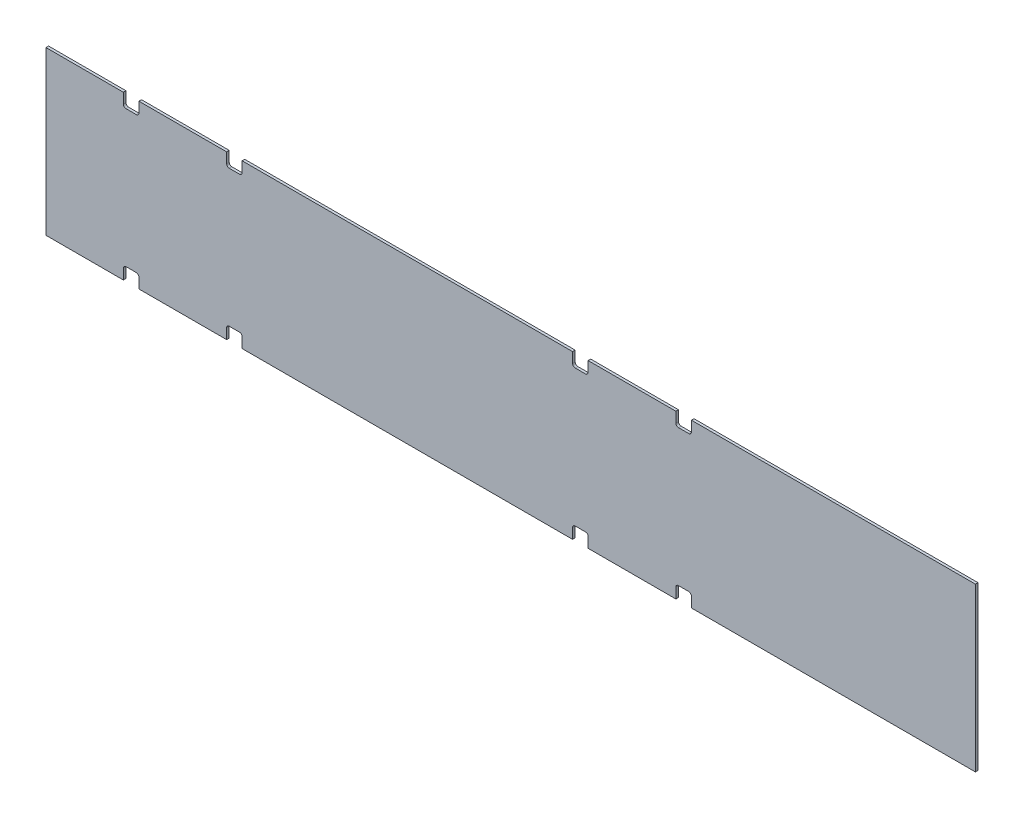
SolidWorks part; units mm, degrees
material "PC High Viscosity"
ref_plane "Front Plane" through (0, 0, 0) normal (0, 0, 1) x (1, 0, 0)
ref_plane "Top Plane" through (0, 0, 0) normal (0, 1, 0) x (1, 0, 0)
ref_plane "Right Plane" through (0, 0, 0) normal (1, 0, 0) x (0, 0, -1)
sketch "Sketch1" plane through (0, 0, 0) normal (0, 0, 1) x (1, 0, 0)
  line L1 (-571.5, -100.0125) -> (571.5, -100.0125)
  line L2 (-571.5, -100.0125) -> (-571.5, 100.0125)
  line L3 (-571.5, 100.0125) -> (571.5, 100.0125)
  line L4 (571.5, -100.0125) -> (571.5, 100.0125)
  line L5 (-571.5, -100.0125) -> (571.5, 100.0125) construction
  line L6 (-571.5, 100.0125) -> (571.5, -100.0125) construction
  point P0 (0, 0)
  dimension "D1" = 1143
  dimension "D2" = 200.025
extrude "Boss-Extrude1" add sketch "Sketch1" along normal blind 3.175
sketch "Sketch3" plane through (0, 0, 3.175) normal (0, 0, 1) x (1, 0, 0)
  line L0 (-571.5, -100.0125) -> (571.5, -100.0125) construction
  line L1 (-476.3389, -100.0125) -> (-457.2889, -100.0125)
  line L2 (-476.3389, -100.0125) -> (-476.3389, -84.1375)
  line L3 (-476.3389, -84.1375) -> (-457.2889, -84.1375)
  line L4 (-349.3389, -100.0125) -> (-349.3389, -84.1375)
  line L5 (-349.3389, -100.0125) -> (-330.2889, -100.0125)
  line L6 (-457.2889, -100.0125) -> (-457.2889, -84.1375)
  line L7 (-571.5, 100.0125) -> (-571.5, -100.0125) construction
  line L8 (-330.2889, -100.0125) -> (-330.2889, -84.1375)
  line L9 (-349.3389, -84.1375) -> (-330.2889, -84.1375)
  line L10 (-476.3389, -100.0125) -> (-349.3389, -100.0125) construction
  line L11 (76.1111, -100.0125) -> (76.1111, -84.1375)
  line L12 (76.1111, -100.0125) -> (95.1611, -100.0125)
  line L13 (95.1611, -100.0125) -> (95.1611, -84.1375)
  line L14 (76.1111, -84.1375) -> (95.1611, -84.1375)
  line L15 (203.1111, -100.0125) -> (203.1111, -84.1375)
  line L16 (203.1111, -84.1375) -> (222.1611, -84.1375)
  line L17 (222.1611, -100.0125) -> (222.1611, -84.1375)
  line L18 (203.1111, -100.0125) -> (222.1611, -100.0125)
  line L19 (-476.3389, -100.0125) -> (76.1111, -100.0125) construction
  point P6 (-466.8139, -100.0125)
  dimension "D1" = 15.875
  dimension "D2" = 19.05
  dimension "D3" = 104.6861
  dimension "D4" = 2
  dimension "D5" = 127
  dimension "D6" = 2
  dimension "D7" = 552.45
extrude "Cut-Extrude1" cut sketch "Sketch3" against normal through all
fillet "Fillet1" radius 3.175 8 edges at (222.1611, -84.1375, 1.5875) (203.1111, -84.1375, 1.5875) (76.1111, -84.1375, 1.5875) (95.1611, -84.1375, 1.5875) (-349.3389, -84.1375, 1.5875) (-330.2889, -84.1375, 1.5875) (-457.2889, -84.1375, 1.5875) (-476.3389, -84.1375, 1.5875)
mirror "Mirror2" about plane through (0, 0, 0) normal (0, 1, 0) of "Fillet1", "Cut-Extrude1"
